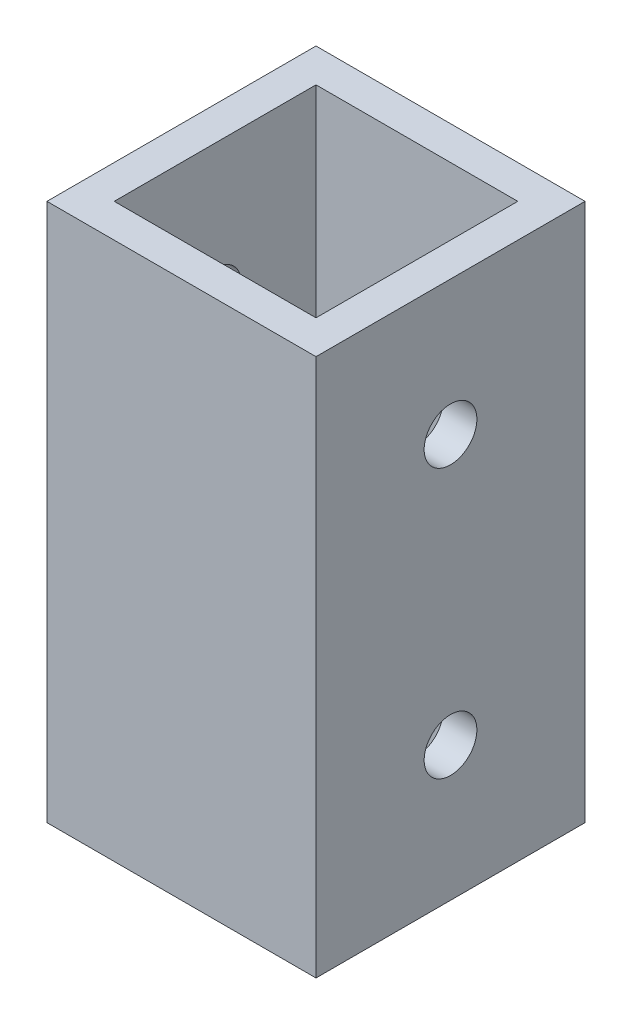
SolidWorks part; units mm, degrees
ref_plane "Front" through (0, 0, 0) normal (0, 0, 1) x (1, 0, 0)
ref_plane "Top" through (0, 0, 0) normal (0, 1, 0) x (1, 0, 0)
ref_plane "Right" through (0, 0, 0) normal (1, 0, 0) x (0, 0, -1)
sketch "Sketch1" plane through (0, 0, 0) normal (0, 1, 0) x (1, 0, 0)
  line L1 (-12.7, -12.7) -> (12.7, -12.7)
  line L2 (-12.7, -12.7) -> (-12.7, 12.7)
  line L3 (-12.7, 12.7) -> (12.7, 12.7)
  line L4 (12.7, -12.7) -> (12.7, 12.7)
  line L5 (-12.7, -12.7) -> (12.7, 12.7) construction
  line L6 (-12.7, 12.7) -> (12.7, -12.7) construction
  point P0 (0, 0)
  dimension "D1" = 25.4
extrude "Extrude-Thin1" add sketch "Sketch1" along normal mid plane 50.8 thin thin type one direction reverse wall 3.175
sketch "Sketch2" plane through (12.7, 0, 0) normal (1, 0, 0) x (0, 0, -1)
  line L0 (0, 25.4) -> (0, -25.4) construction
  line L1 (-12.7, 25.4) -> (12.7, 25.4) construction
  line L2 (-12.7, -25.4) -> (12.7, -25.4) construction
  circle A0 centre (0, 12.7) radius 2.4892
  circle A1 centre (0, -12.7) radius 2.4892
  dimension "D1" = 4.9784
  dimension "D2" = 12.7
  dimension "D3" = 25.4
extrude "Cut-Extrude1" cut sketch "Sketch2" against normal through all
